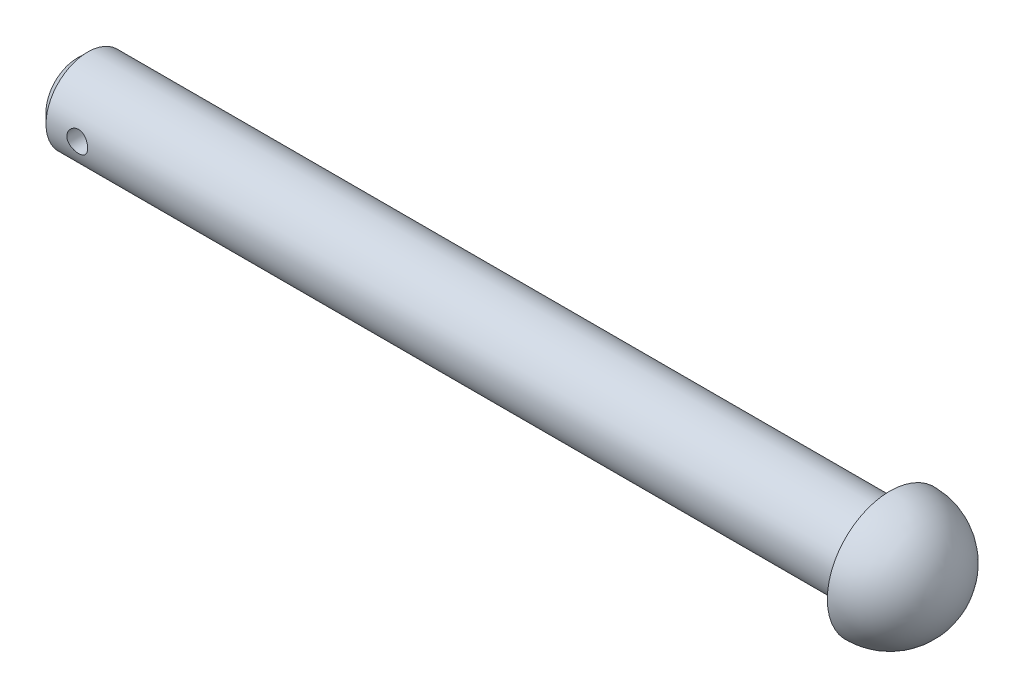
SolidWorks part; units mm, degrees
ref_plane "Front Plane" through (0, 0, 0) normal (0, 0, 1) x (1, 0, 0)
ref_plane "Top Plane" through (0, 0, 0) normal (0, 1, 0) x (1, 0, 0)
ref_plane "Right Plane" through (0, 0, 0) normal (1, 0, 0) x (0, 0, -1)
sketch "Sketch1" plane through (0, 0, 0) normal (0, 0, 1) x (1, 0, 0)
  line L0 (0, 0) -> (42, 0) construction
  line L1 (0, 0) -> (0, 1.5)
  line L2 (0, 1.5) -> (0.5, 2)
  line L3 (0.5, 2) -> (39, 2)
  line L4 (39, 2) -> (39, 3)
  line L5 (0, 0) -> (42, 0)
  arc A0 (39, 3) -> (42, 0) centre (39, 0) cw
  dimension "D5" = 3
  dimension "D1" = 2
  dimension "D2" = 0.5
  dimension "D3" = 0.5
  dimension "D4" = 39
  dimension "D6" = 3
revolve "Revolve1" add sketch "Sketch1" angle 360 about L0
sketch "Sketch2" plane through (0, 0, 0) normal (0, 0, 1) x (1, 0, 0)
  line L0 (39, 2) -> (39, -2) construction
  circle A0 centre (2, 0) radius 0.5
  dimension "D1" = 1
  dimension "D2" = 37
extrude "Cut-Extrude1" cut sketch "Sketch2" against normal through all both and the other way through all
